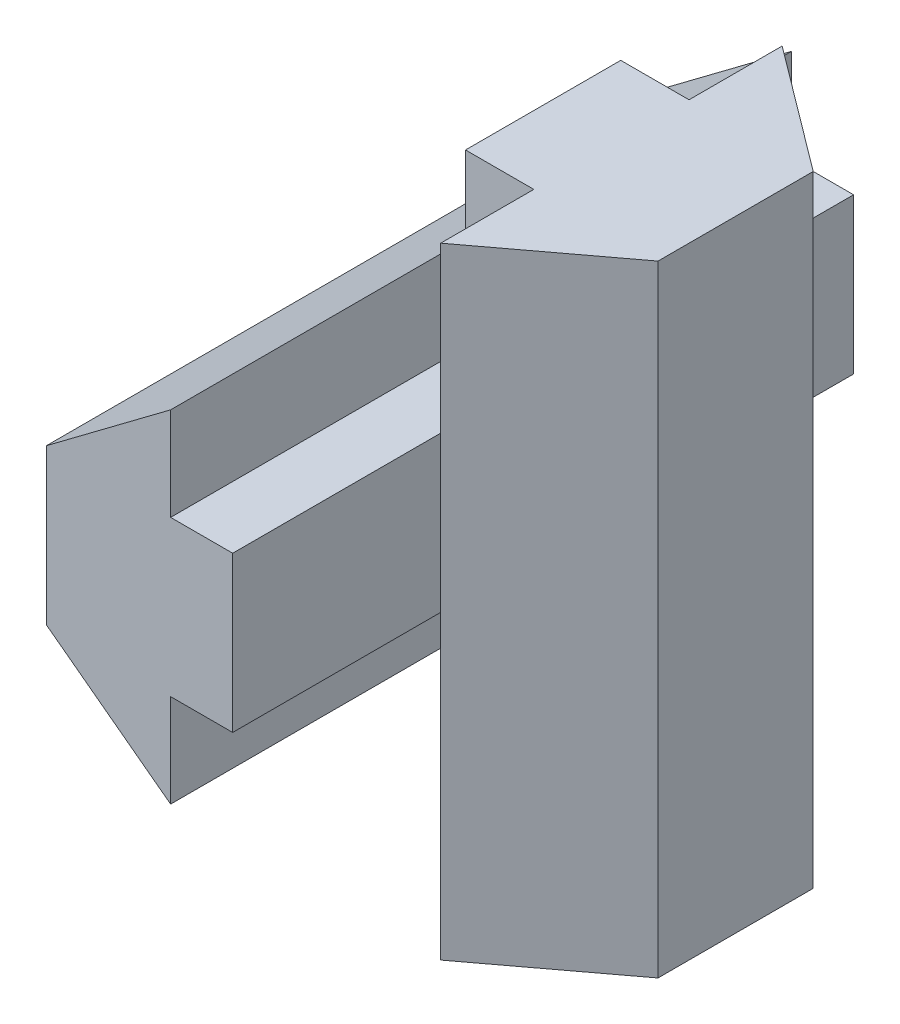
SolidWorks part; units mm, degrees
ref_plane "Plan de face" through (0, 0, 0) normal (0, 0, 1) x (1, 0, 0)
ref_plane "Plan de dessus" through (0, 0, 0) normal (0, 1, 0) x (1, 0, 0)
ref_plane "Plan de droite" through (0, 0, 0) normal (1, 0, 0) x (0, 0, -1)
sketch "ProfileRainureEsquisse" plane through (0, 0, 0) normal (0, 0, 1) x (1, 0, 0)
  line L0 (0, -2.5) -> (0, 2.5)
  line L1 (0, 2.5) -> (4, 5.5)
  line L2 (0, -2.5) -> (4, -5.5)
  line L3 (4, 5.5) -> (4, 2.5)
  line L4 (4, 2.5) -> (6, 2.5)
  line L5 (6, 2.5) -> (6, -2.5)
  line L6 (6, -2.5) -> (4, -2.5)
  line L7 (4, -2.5) -> (4, -5.5)
  point P4 (0, 0)
  dimension "D1" = 4
  dimension "D2" = 6
  dimension "D3" = 5
  dimension "D4" = 8
extrude "Boss.-Extru.1" add sketch "ProfileRainureEsquisse" along normal mid plane 20
sketch "Esquisse1" plane through (0, 0, 0) normal (0, 1, 0) x (1, 0, 0)
  line L0 (6, 2.5) -> (8.2, 2.5)
  line L1 (8.2, 2.5) -> (8.2, 5.5)
  line L2 (8.2, 5.5) -> (12.2, 2.5)
  line L3 (12.2, 2.5) -> (12.2, -2.5)
  line L4 (8.2, -2.5) -> (8.2, -5.5)
  line L5 (8.2, -2.5) -> (6, -2.5)
  line L6 (6, -2.5) -> (6, 2.5)
  line L7 (6, -10) -> (6, 10) construction
  line L8 (8.2, -5.5) -> (12.2, -2.5)
  point P6 (6, 0)
  point P11 (6, 0)
  point P12 (8.1712, 0.6867)
  dimension "D1" = 2.2
  dimension "D2" = 4
  dimension "D3" = 8
  dimension "D4" = 5
extrude "Boss.-Extru.2" add sketch "Esquisse1" along normal mid plane 20
